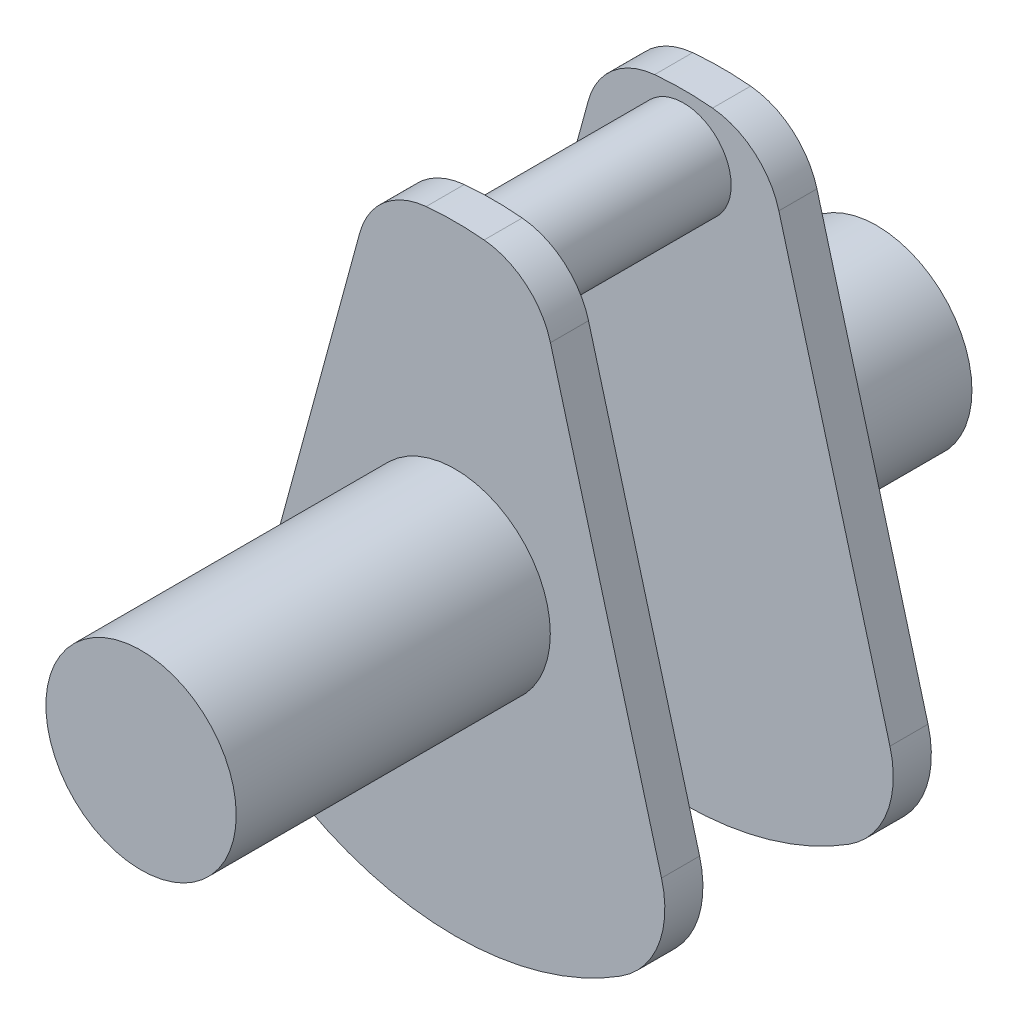
SolidWorks part; units mm, degrees
ref_plane "Front Plane" through (0, 0, 0) normal (0, 0, 1) x (1, 0, 0)
ref_plane "Top Plane" through (0, 0, 0) normal (0, 1, 0) x (1, 0, 0)
ref_plane "Right Plane" through (0, 0, 0) normal (1, 0, 0) x (0, 0, -1)
sketch "Sketch1" plane through (0, 0, 0) normal (0, 0, 1) x (1, 0, 0)
  line L0 (0, 6.5) -> (0, -6.5) construction
  line L1 (-2.0028, 5.2986) -> (-4.3368, -3.2769)
  line L2 (2.0028, 5.2986) -> (4.3368, -3.2769)
  arc A0 (-3.4768, -5.492) -> (3.4768, -5.492) centre (0, 0) ccw
  arc A1 (0.6089, 6.4714) -> (-0.6089, 6.4714) centre (0, 0) ccw
  arc A2 (2.0028, 5.2986) -> (0.6089, 6.4714) centre (0.459, 4.8785) ccw
  arc A3 (-2.0028, 5.2986) -> (-0.6089, 6.4714) centre (-0.459, 4.8785) cw
  arc A4 (3.4768, -5.492) -> (4.3368, -3.2769) centre (2.407, -3.8022) ccw
  arc A5 (-4.3368, -3.2769) -> (-3.4768, -5.492) centre (-2.407, -3.8022) ccw
  point P10 (1.7405, 6.2626)
  point P13 (-1.7405, 6.2626)
  point P16 (4.6742, -4.5168)
  point P19 (-4.6742, -4.5168)
  dimension "D1" = 13
  dimension "D4" = 1.6
  dimension "D5" = 2
  dimension "D2" = 30.45
  dimension "D3" = 0.918
extrude "Boss-Extrude1" add sketch "Sketch1" along normal blind 0.8
sketch "Sketch2" plane through (0, 0, 0.8) normal (0, 0, 1) x (1, 0, 0)
  line L0 (0, 6.5) -> (0, 5.26) construction
  arc A0 (0.6089, 6.4714) -> (-0.6089, 6.4714) centre (0, 0) ccw construction
  circle A1 centre (0, 5.26) radius 1
  dimension "D1" = 2
  dimension "D2" = 5.26
extrude "Boss-Extrude2" add sketch "Sketch2" along normal blind 2
sketch "Sketch3" plane through (0, 0, 0) normal (0, 0, -1) x (-1, 0, 0)
  circle A0 centre (0, 0) radius 2
  dimension "D1" = 4
extrude "Boss-Extrude3" add sketch "Sketch3" along normal blind 3.26
mirror "Mirror1" about plane through (0, 5.26, 2.8) normal (0, 0, 1) of bodies 103
sketch "Sketch6" plane through (0, 0, 8.86) normal (0, 0, 1) x (1, 0, 0)
  circle A1 centre (0, 0) radius 2
  circle A2 centre (0, 0) radius 2
  dimension "D1" = 0
extrude "Boss-Extrude4" add sketch "Sketch6" along normal blind 3.34
